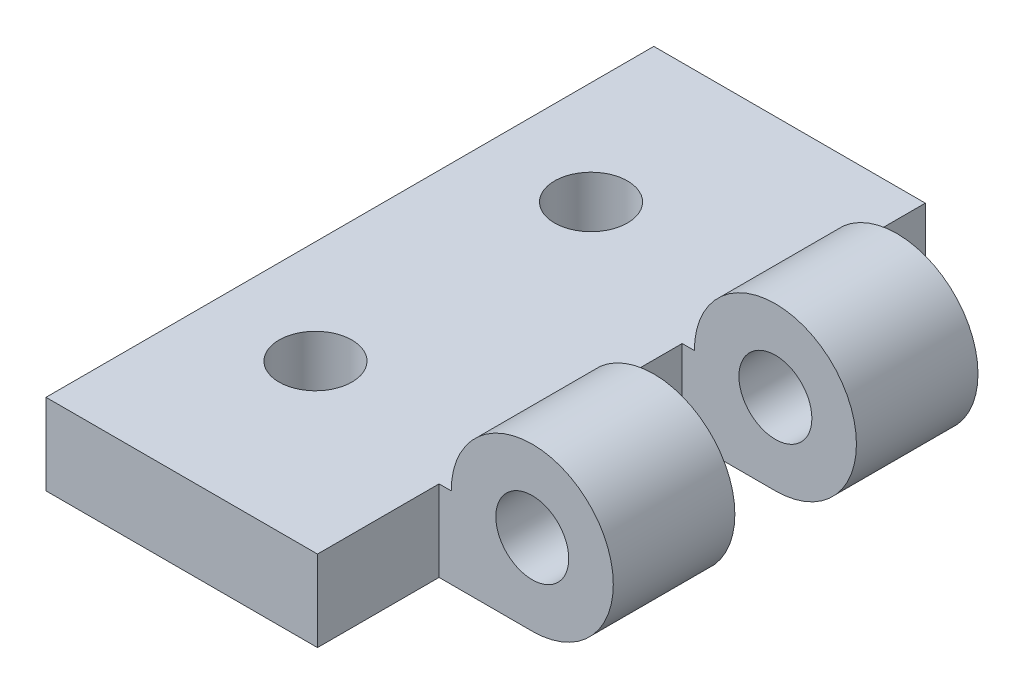
SolidWorks part; units mm, degrees
ref_plane "Front Plane" through (0, 0, 0) normal (0, 0, 1) x (1, 0, 0)
ref_plane "Top Plane" through (0, 0, 0) normal (0, 1, 0) x (1, 0, 0)
ref_plane "Right Plane" through (0, 0, 0) normal (1, 0, 0) x (0, 0, -1)
sketch "Sketch1" plane through (0, 0, 0) normal (0, 0, 1) x (1, 0, 0)
  line L0 (0, 0) -> (0, 5.08)
  line L1 (0, 0) -> (22.86, 0)
  line L5 (0, 5.08) -> (17.78, 5.08)
  arc A0 (22.86, 0) -> (17.78, 5.08) centre (22.86, 5.08) ccw
  dimension "D1" = 10.16
  dimension "D2" = 5.08
  dimension "D3" = 17.78
extrude "Boss-Extrude1" add sketch "Sketch1" along normal blind 38.1
sketch "Sketch3" plane through (0, 5.08, 0) normal (0, 1, 0) x (1, 0, 0)
  line L0 (6.477, -8.128) -> (6.477, 0) construction
  line L1 (17.78, 0) -> (0, 0) construction
  line L2 (6.477, -12.7) -> (6.477, -25.4) construction
  line L3 (6.477, -29.972) -> (6.477, -38.1) construction
  line L5 (17.78, -38.1) -> (0, -38.1) construction
  line L6 (17.78, -38.1) -> (17.78, 0) construction
  circle A0 centre (6.477, -10.414) radius 2.286
  circle A1 centre (6.477, -27.686) radius 2.286
  dimension "D1" = 4.572
  dimension "D2" = 11.303
  dimension "D3" = 12.7
extrude "Cut-Extrude2" cut sketch "Sketch3" against normal through all
sketch "Sketch4" plane through (0, 5.08, 0) normal (0, 1, 0) x (1, 0, 0)
  line L0 (17.78, 0) -> (0, 0) construction
  line L1 (17.018, 0) -> (27.94, 0)
  line L2 (17.018, 0) -> (17.018, -7.62)
  line L3 (17.018, -7.62) -> (27.94, -7.62)
  line L4 (27.94, 0) -> (27.94, -7.62)
  line L5 (27.94, -38.1) -> (27.94, 0) construction
  line L6 (17.78, -38.1) -> (17.78, 0) construction
  line L7 (27.94, -38.1) -> (17.018, -38.1)
  line L8 (27.94, -38.1) -> (27.94, -30.48)
  line L9 (27.94, -30.48) -> (17.018, -30.48)
  line L10 (17.018, -38.1) -> (17.018, -30.48)
  line L11 (17.018, -7.62) -> (17.018, -15.24) construction
  line L12 (27.94, -22.86) -> (17.018, -22.86)
  line L13 (27.94, -22.86) -> (27.94, -15.24)
  line L14 (27.94, -15.24) -> (17.018, -15.24)
  line L15 (17.018, -22.86) -> (17.018, -15.24)
  line L16 (17.018, -30.48) -> (17.018, -22.86) construction
  dimension "D1" = 0.762
  dimension "D2" = 0.762
  dimension "D3" = 7.62
  dimension "D4" = 7.62
  dimension "D5" = 0.762
  dimension "D6" = 7.62
extrude "Cut-Extrude3" cut sketch "Sketch4" against normal through all both and the other way through all
sketch "Sketch7" plane through (0, 0, 30.48) normal (0, 0, 1) x (1, 0, 0)
  circle A0 centre (22.86, 5.08) radius 2.286
  dimension "D1" = 4.572
extrude "Cut-Extrude4" cut sketch "Sketch7" against normal through all
